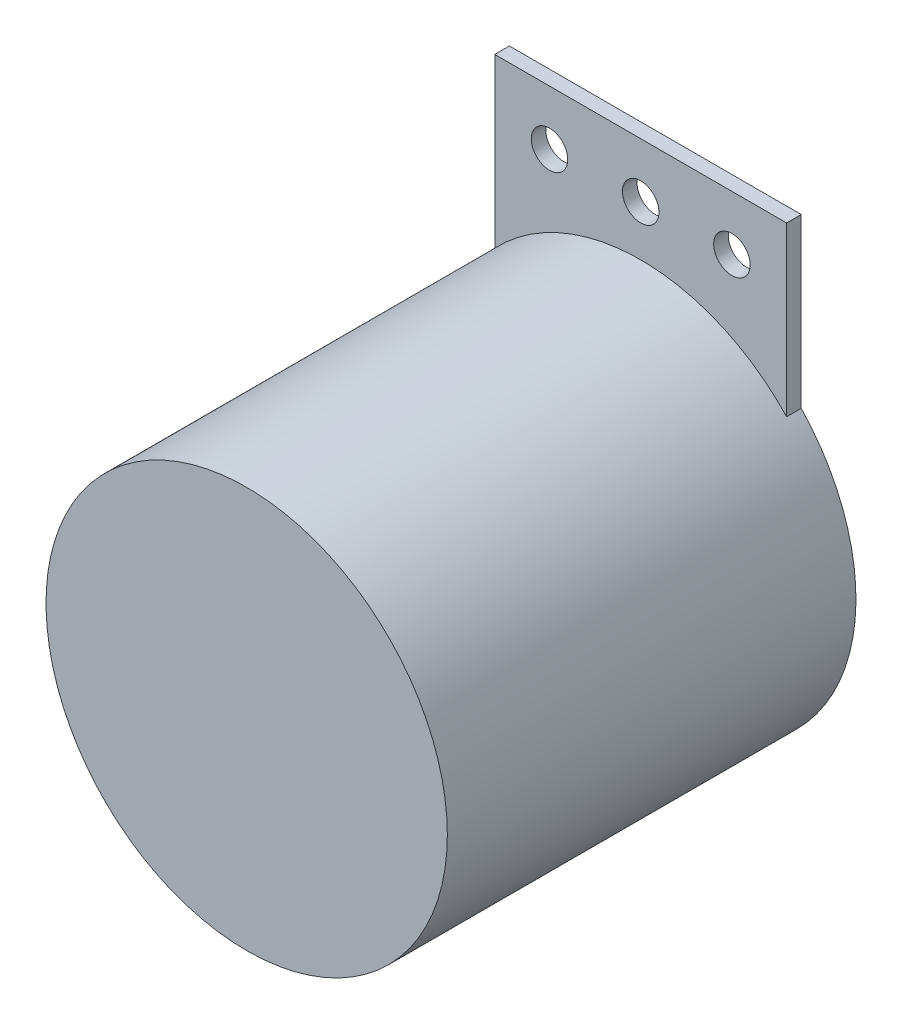
SolidWorks part; units mm, degrees
ref_plane "前视基准面" through (0, 0, 0) normal (0, 0, 1) x (1, 0, 0)
ref_plane "上视基准面" through (0, 0, 0) normal (0, 1, 0) x (1, 0, 0)
ref_plane "右视基准面" through (0, 0, 0) normal (1, 0, 0) x (0, 0, -1)
sketch "草图1" plane through (0, 0, 0) normal (0, 0, 1) x (1, 0, 0)
  circle A0 centre (0, 0) radius 27.5
extrude "凸台-拉伸1" add sketch "草图1" along normal blind 56
sketch "草图2" plane through (0, 0, 0) normal (0, 0, -1) x (-1, 0, 0)
  line L1 (-20, 41.8746) -> (-20, 18.8746)
  line L3 (-20, 18.8746) -> (20, 18.8746)
  line L4 (20, 18.8746) -> (20, 41.8746)
  line L5 (20, 41.8746) -> (-20, 41.8746)
  circle A0 centre (0, 0) radius 27.5 construction
extrude "凸台-拉伸2" add sketch "草图2" against normal blind 2
sketch "草图3" plane through (0, 0, 2) normal (0, 0, 1) x (1, 0, 0)
  circle A0 centre (0, 34.3746) radius 2.5
  circle A1 centre (-12.5, 34.3746) radius 2.5
  circle A2 centre (12.5, 34.3746) radius 2.5
extrude "切除-拉伸1" cut sketch "草图3" against normal blind 2
